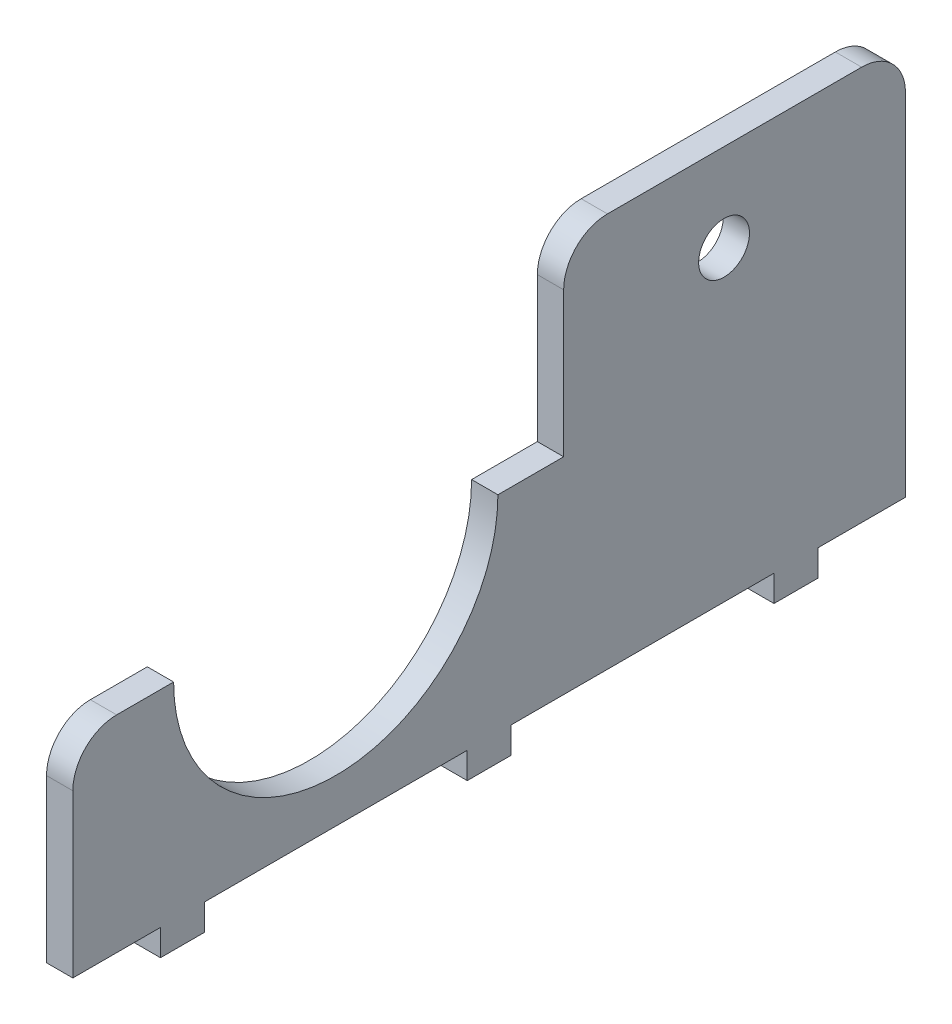
SolidWorks part; units mm, degrees
ref_plane "Front Plane" through (0, 0, 0) normal (0, 0, 1) x (1, 0, 0)
ref_plane "Top Plane" through (0, 0, 0) normal (0, 1, 0) x (1, 0, 0)
ref_plane "Right Plane" through (0, 0, 0) normal (1, 0, 0) x (0, 0, -1)
ref_plane "Plane2" through (0, -2, 0) normal (0, 1, 0) x (1, 0, 0)
sketch "Sketch1" plane through (0, 0, 0) normal (1, 0, 0) x (0, 0, -1)
  line L0 (-36, 11.75) -> (-47.5, 11.75)
  line L1 (47.5, -11.75) -> (-47.5, -11.75)
  line L2 (47.5, -11.75) -> (47.5, 11.75)
  line L3 (47.5, 11.75) -> (1, 11.75)
  line L4 (-47.5, -11.75) -> (-47.5, 11.75)
  line L5 (47.5, -11.75) -> (-47.5, 11.75) construction
  line L6 (47.5, 11.75) -> (-47.5, -11.75) construction
  arc A0 (-36, 11.75) -> (1, 11.75) centre (-17.5, 11.75) ccw
  point P0 (0, 0)
  dimension "D1" = 37
  dimension "D2" = 95
  dimension "D3" = 23.5
  dimension "D4" = 23.5
  dimension "D5" = 30
extrude "Boss-Extrude1" add sketch "Sketch1" along normal blind 3
sketch "Sketch3" plane through (0, -11.75, 0) normal (0, -1, 0) x (1, 0, 0)
  line L0 (0, 47.5) -> (0, -47.5) construction
  line L5 (3, 47.5) -> (3, -47.5) construction
  line L7 (3, 47.5) -> (0, 47.5) construction
  line L8 (0, -37.5) -> (3, -37.5)
  line L9 (0, -37.5) -> (0, -32.5)
  line L10 (0, -32.5) -> (3, -32.5)
  line L11 (3, -37.5) -> (3, -32.5)
  line L16 (0, -2.5) -> (3, -2.5)
  line L17 (0, -2.5) -> (0, 2.5)
  line L18 (0, 2.5) -> (3, 2.5)
  line L19 (3, -2.5) -> (3, 2.5)
  line L20 (0, 37.5) -> (3, 37.5)
  line L21 (0, 37.5) -> (0, 32.5)
  line L22 (0, 32.5) -> (3, 32.5)
  line L23 (3, 37.5) -> (3, 32.5)
  point P22 (1.5, 2.5)
  dimension "D1" = 10
  dimension "D3" = 5
  dimension "D4" = 30
  dimension "D5" = 5
  dimension "D6" = 5
  dimension "D7" = 30
extrude "Boss-Extrude2" add sketch "Sketch3" along normal blind 3
sketch "Sketch5" plane through (0, 11.75, 0) normal (0, 1, 0) x (1, 0, 0)
  line L0 (0, 47.5) -> (0, 1) construction
  line L1 (3, 47.5) -> (0, 47.5)
  line L2 (3, 47.5) -> (3, 8.5)
  line L3 (3, 8.5) -> (0, 8.5)
  line L4 (0, 47.5) -> (0, 8.5)
  line L5 (3, 1) -> (0, 1) construction
  dimension "D1" = 7.5
extrude "Boss-Extrude3" add sketch "Sketch5" along normal blind 21.5
sketch "Sketch7" plane through (0, 0, 0) normal (-1, 0, 0) x (0, 0, 1)
  line L0 (-37.5, -11.75) -> (-47.5, -11.75) construction
  line L2 (47.5, 11.75) -> (47.5, -11.75) construction
  arc A0 (-29.7, 23.25) -> (-23.9, 23.25) centre (-26.8, 23.25) ccw
  arc A1 (-29.7, 23.25) -> (-23.9, 23.25) centre (-26.8, 23.25) cw
  dimension "D1" = 5.8
  dimension "D2" = 35
  dimension "D3" = 74.3
extrude "Cut-Extrude3" cut sketch "Sketch7" against normal through all
fillet "Fillet1" radius 5 3 edges at (1.5, 33.25, -8.5) (1.5, 33.25, -47.5) (1.5, 11.75, 47.5)
